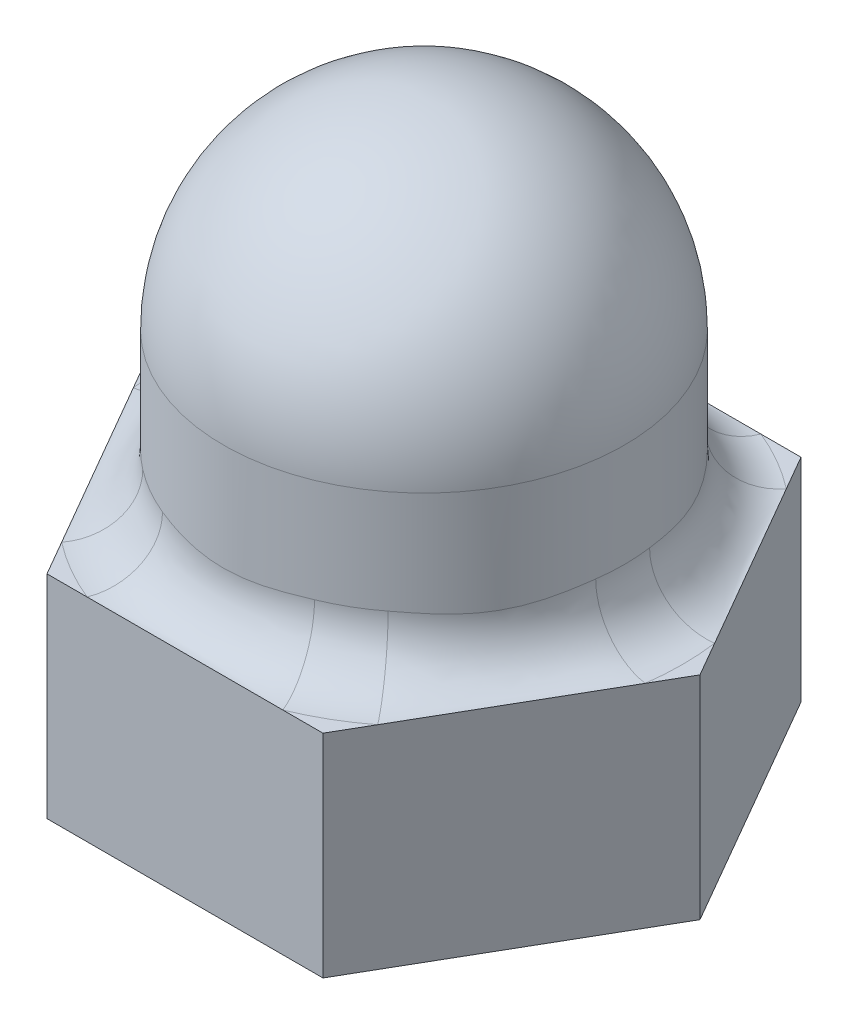
SolidWorks part; units mm, degrees
material "Alloy Steel"
ref_plane "Front Plane" through (0, 0, 0) normal (0, 0, 1) x (1, 0, 0)
ref_plane "Top Plane" through (0, 0, 0) normal (0, 1, 0) x (1, 0, 0)
ref_plane "Right Plane" through (0, 0, 0) normal (1, 0, 0) x (0, 0, -1)
sketch "Sketch1" plane through (0, 0, 0) normal (0, 0, 1) x (1, 0, 0)
  line L0 (0, 0) -> (0, 9.4488) construction
  line L1 (0, 0) -> (0, 9.4488)
  line L2 (-3.302, 0) -> (-3.302, 6.1468)
  line L3 (-3.302, 0) -> (0, 0)
  line L4 (-3.302, 0) -> (-3.302, 9.4488) construction
  arc A0 (-3.302, 6.1468) -> (0, 9.4488) centre (0, 6.1468) cw
  point P3 (3.302, 0)
  point P4 (3.302, 9.4488)
  dimension "D1" = 9.4488
  dimension "D3" = 3.302
revolve "Revolve2" add sketch "Sketch1" angle 360 about L1
sketch "Sketch2" plane through (0, 0, 0) normal (0, -1, 0) x (1, 0, 0)
  line L1 (4.5461, 0) -> (2.273, 3.937)
  line L2 (2.273, 3.937) -> (-2.273, 3.937)
  line L3 (-2.273, 3.937) -> (-4.5461, 0)
  line L4 (-4.5461, 0) -> (-2.273, -3.937)
  line L5 (-2.273, -3.937) -> (2.273, -3.937)
  line L6 (2.273, -3.937) -> (4.5461, 0)
  circle A0 centre (0, 0) radius 3.937 construction
  dimension "D1" = 7.874
extrude "Boss-Extrude1" add sketch "Sketch2" against normal blind 3.4925
hole_wizard "#12-28 Tapped Hole1" positions "Sketch4" profile "Sketch3" tap size "#12-28" standard "Ansi Inch"
sketch "Sketch4" plane through (0, 0, 0) normal (0, -1, 0) x (1, 0, 0)
  point P1 (0, 0)
sketch "Sketch3" plane through (0, 0, 0) normal (1, 0, 0) x (0, 0, -1)
  line L0 (0, 0) -> (0, 8.0276)
  line L1 (0, 8.0276) -> (2.3114, 7.62)
  line L2 (2.3114, 7.62) -> (2.3114, 0)
  line L5 (2.3114, 0) -> (0, 0)
  line L10 (0, 8.0276) -> (-2.3114, 7.62) construction
  line L11 (0, -6.35) -> (0, 107.95) construction
  dimension "Tap Drill Dia." = 4.6228
  dimension "Tap Drill Depth" = 7.62
  dimension "Drill Angle" = 160
cosmetic thread "Hole Thread1" parameters "D1"=7.62, "D2"=5.4864
fillet "Fillet2" radius 0.9525 1 edges at (0, 3.4925, -3.302)
